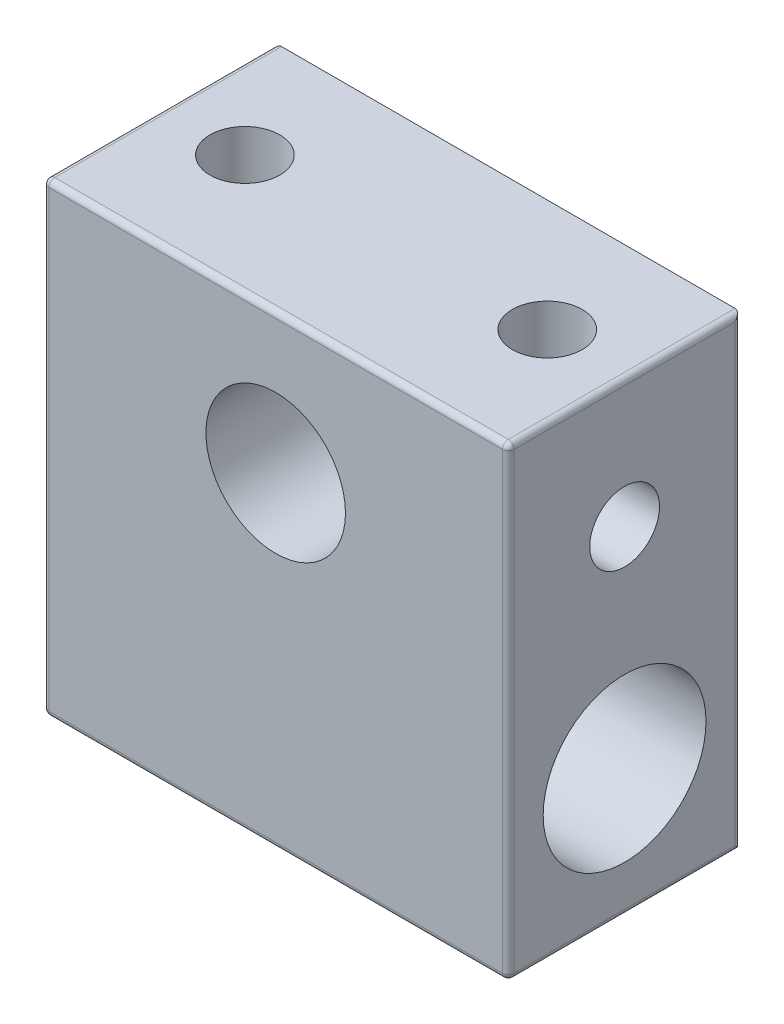
SolidWorks part; units mm, degrees
ref_plane "Front Plane" through (0, 0, 0) normal (0, 0, 1) x (1, 0, 0)
ref_plane "Top Plane" through (0, 0, 0) normal (0, 1, 0) x (1, 0, 0)
ref_plane "Right Plane" through (0, 0, 0) normal (1, 0, 0) x (0, 0, -1)
sketch "Sketch1" plane through (0, 0, 0) normal (0, 0, 1) x (1, 0, 0)
  line L1 (-10, 10) -> (10, 10)
  line L2 (-10, 10) -> (-10, -10)
  line L3 (-10, -10) -> (10, -10)
  line L4 (10, 10) -> (10, -10)
  line L5 (-10, 10) -> (10, -10) construction
  line L6 (-10, -10) -> (10, 10) construction
  point P0 (0, 0)
  dimension "D1" = 20
extrude "Boss-Extrude1" add sketch "Sketch1" along normal blind 10
fillet "Fillet1" radius 0.25 10 edges at (-10, 0, 0) (10, 0, 0) (0, -10, 10) (-10, 0, 10) (0, 10, 10) (10, 0, 10) (10, 10, 5) (10, -10, 5) (-10, 10, 5) (-10, -10, 5)
sketch "Sketch2" plane through (0, 0, 10) normal (0, 0, 1) x (1, 0, 0)
  line L0 (-9.75, 10) -> (9.75, 10) construction
  circle A0 centre (0, 4) radius 3
  dimension "D1" = 6
  dimension "D2" = 6
extrude "Cut-Extrude1" cut sketch "Sketch2" against normal blind 10
sketch "Sketch3" plane through (-10, 0, 0) normal (-1, 0, 0) x (0, 0, 1)
  line L0 (9.75, -10) -> (0, -10) construction
  line L3 (10, 9.75) -> (10, -9.75) construction
  circle A1 centre (5, -4.5) radius 3.5
  dimension "D1" = 7
  dimension "D2" = 5.5
  dimension "D6" = 5
extrude "Cut-Extrude2" cut sketch "Sketch3" against normal blind 20
sketch "Sketch4" plane through (-10, 0, 0) normal (-1, 0, 0) x (0, 0, 1)
  line L0 (10, 9.75) -> (10, -9.75) construction
  line L1 (0, 10) -> (9.75, 10) construction
  circle A0 centre (5, 4.5) radius 1.5
  dimension "D3" = 3
  dimension "D1" = 5
  dimension "D2" = 5.5
extrude "Cut-Extrude3" cut sketch "Sketch4" against normal blind 6.5
sketch "Sketch5" plane through (10, 0, 0) normal (1, 0, 0) x (0, 0, -1)
  line L0 (-9.75, 10) -> (0, 10) construction
  line L1 (-10, -9.75) -> (-10, 9.75) construction
  circle A0 centre (-5, 4.5) radius 1.5
  dimension "D1" = 3
  dimension "D2" = 5.5
  dimension "D3" = 5
extrude "Cut-Extrude4" cut sketch "Sketch5" against normal blind 6.5
sketch "Sketch6" plane through (0, 10, 0) normal (0, 1, 0) x (1, 0, 0)
  line L0 (9.75, 0) -> (-9.75, 0) construction
  circle A0 centre (-6.5, -4.8241) radius 1.5
  circle A1 centre (6.5, -4.8241) radius 1.5
  point P4 (0, 0)
  dimension "D2" = 3
  dimension "D3" = 3
  dimension "D1" = 13
  dimension "D4" = 6.5
extrude "Cut-Extrude5" cut sketch "Sketch6" against normal blind 6
